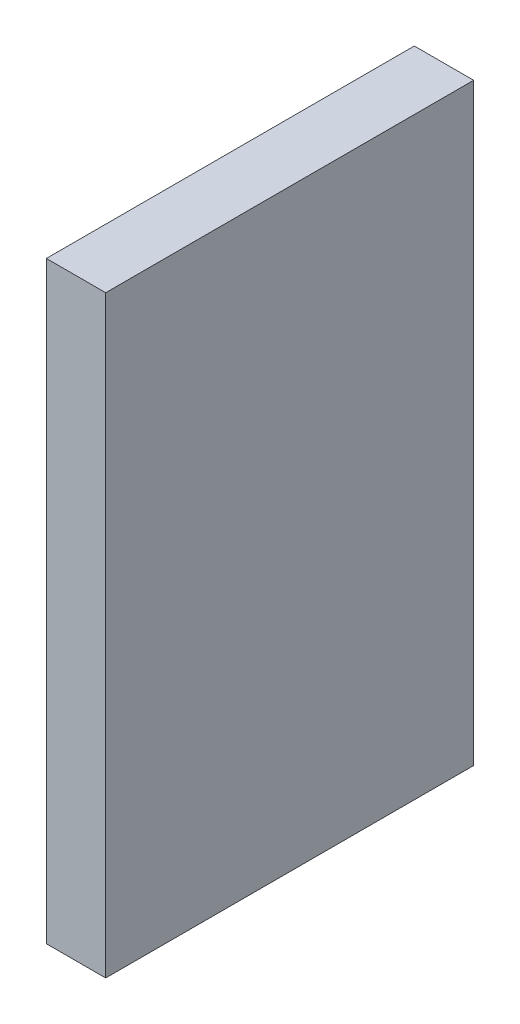
SolidWorks part; units mm, degrees
ref_plane "Alzado" through (0, 0, 0) normal (0, 0, 1) x (1, 0, 0)
ref_plane "Planta" through (0, 0, 0) normal (0, 1, 0) x (1, 0, 0)
ref_plane "Vista lateral" through (0, 0, 0) normal (1, 0, 0) x (0, 0, -1)
sketch "Croquis1" plane through (0, 0, 0) normal (1, 0, 0) x (0, 0, -1)
  line L0 (9.6977, -14.2045) -> (9.6977, 15.7955)
  line L1 (9.6977, 15.7955) -> (-8.9023, 15.7955)
  line L2 (-8.9023, 15.7955) -> (-8.9023, -14.2045)
  line L3 (-8.9023, -14.2045) -> (9.6977, -14.2045)
extrude "Saliente-Extruir1" add sketch "Croquis1" along normal blind 3
